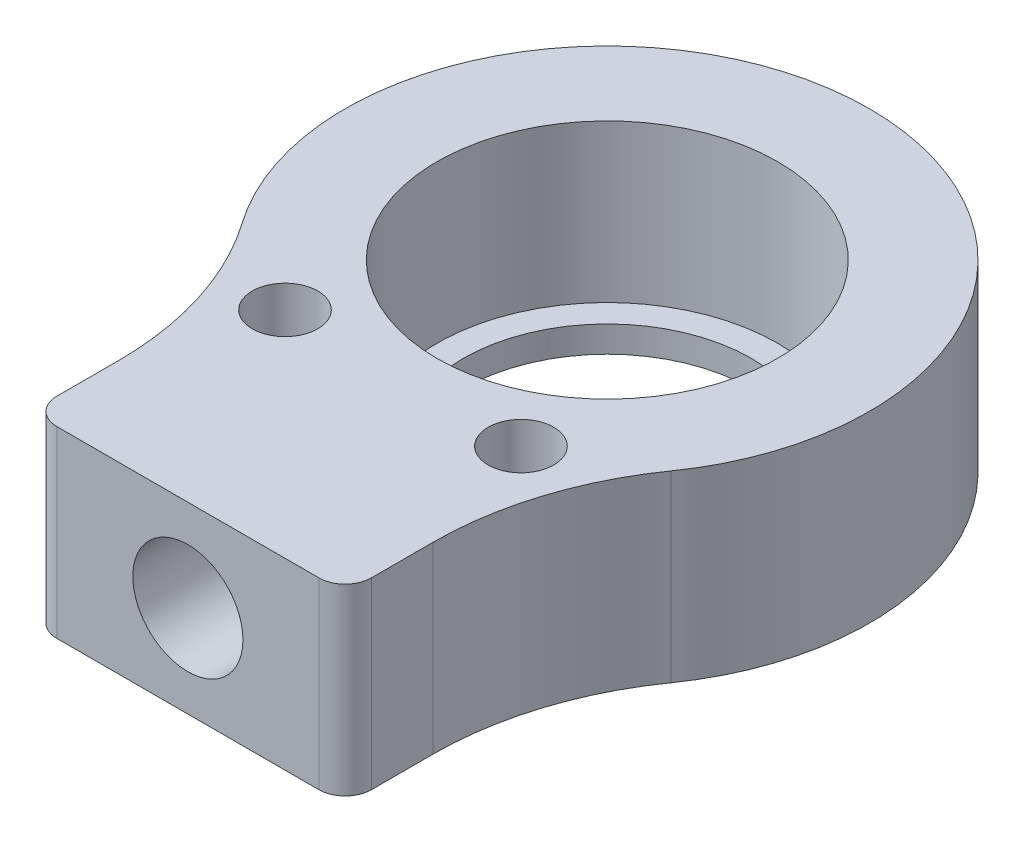
SolidWorks part; units mm, degrees
ref_plane "Plan de face" through (0, 0, 0) normal (0, 0, 1) x (1, 0, 0)
ref_plane "Plan de dessus" through (0, 0, 0) normal (0, 1, 0) x (1, 0, 0)
ref_plane "Plan de droite" through (0, 0, 0) normal (1, 0, 0) x (0, 0, -1)
sketch "Esquisse1" plane through (0, 0, 0) normal (0, 1, 0) x (1, 0, 0)
  circle A0 centre (0, 0) radius 5.5
  circle A1 centre (0, 0) radius 6.5 construction
  circle A2 centre (0, 0) radius 10
  dimension "D1" = 11
  dimension "D2" = 13
  dimension "D3" = 20
extrude "Boss.-Extru.1" add sketch "Esquisse1" along normal blind 7
sketch "Esquisse2" plane through (0, 7, 0) normal (0, 1, 0) x (1, 0, 0)
  circle A0 centre (0, 0) radius 6.5
  dimension "D1" = 13
extrude "Enlèv. mat.-Extru.1" cut sketch "Esquisse2" against normal blind 6
sketch "Esquisse7" plane through (0, 0, 0) normal (0, 1, 0) x (1, 0, 0)
  line L0 (6, -16) -> (-6, -16)
  line L1 (-6, -16) -> (-6, -8)
  line L2 (-6, -8) -> (6, -8)
  line L3 (6, -8) -> (6, -16)
  circle A0 centre (0, 0) radius 10 construction
  point P0 (0, -8)
  point P7 (0, 0)
  dimension "D1" = 12
  dimension "D2" = 8
extrude "Boss.-Extru.2" add sketch "Esquisse7" along normal blind 7
fillet "Congé1" radius 12 2 edges at (-6, 3.5, 8) (6, 3.5, 8)
hole_wizard "Trou taraudé M31" positions "Esquisse5" profile "Esquisse6" tap size "M3" standard "ISO" end condition through all
sketch "Esquisse5" plane through (0, 7, 0) normal (0, 1, 0) x (1, 0, 0)
  line L0 (-4.5, -7.7942) -> (0, 0) construction
  line L1 (0, 0) -> (4.5, -7.7942) construction
  circle A0 centre (0, 0) radius 9 construction
  point P5 (-4.5, -7.7942)
  point P7 (4.5, -7.7942)
  dimension "D1" = 18
  dimension "D2" = 60
sketch "Esquisse6" plane through (4.5, 7, 7.7942) normal (1, 0, 0) x (0, 0, 1)
  line L0 (0, 0) -> (0, 7)
  line L1 (0, 7) -> (1.25, 7)
  line L2 (1.25, 7) -> (1.25, 0)
  line L5 (1.25, 0) -> (0, 0)
  line L11 (0, -6.35) -> (0, 107.95) construction
  dimension "Diamètre du trou pour taraudage jusqu'au prochain" = 2.5
  dimension "Profondeur du trou pour taraudage jusqu'au prochain" = 7
cosmetic thread "Filetage de perçage1" parameters "D1"=15.45, "D2"=3.5
cosmetic thread "Filetage de perçage2" parameters "D1"=7, "D2"=3.5
hole_wizard "Trou taraudé M51" positions "Esquisse8" profile "Esquisse9" tap size "M5" standard "ISO"
sketch "Esquisse8" plane through (0, 0, 16) normal (0, 0, 1) x (1, 0, 0)
  line L0 (-6, 0) -> (6, 0) construction
  point P0 (0, 3.5)
  point P3 (0.8721, 3.8611)
  dimension "D1" = 3.5
cosmetic thread "Filetage de perçage3" parameters "D1"=12, "D2"=5
sketch "Esquisse9" plane through (0, 3.5, 16) normal (1, 0, 0) x (0, -1, 0)
  line L0 (0, 0) -> (0, 17.2618)
  line L1 (0, 17.2618) -> (2.1, 16)
  line L2 (2.1, 16) -> (2.1, 0)
  line L5 (2.1, 0) -> (0, 0)
  line L10 (0, 17.2618) -> (-2.1, 16) construction
  line L11 (0, -6.35) -> (0, 107.95) construction
  dimension "Diamètre du trou pour taraudage" = 4.2
  dimension "Profondeur du trou pour taraudage" = 16
  dimension "Angle de pointe" = 118
fillet "Congé2" radius 1 2 edges at (-6, 3.5, 16) (6, 3.5, 16)
